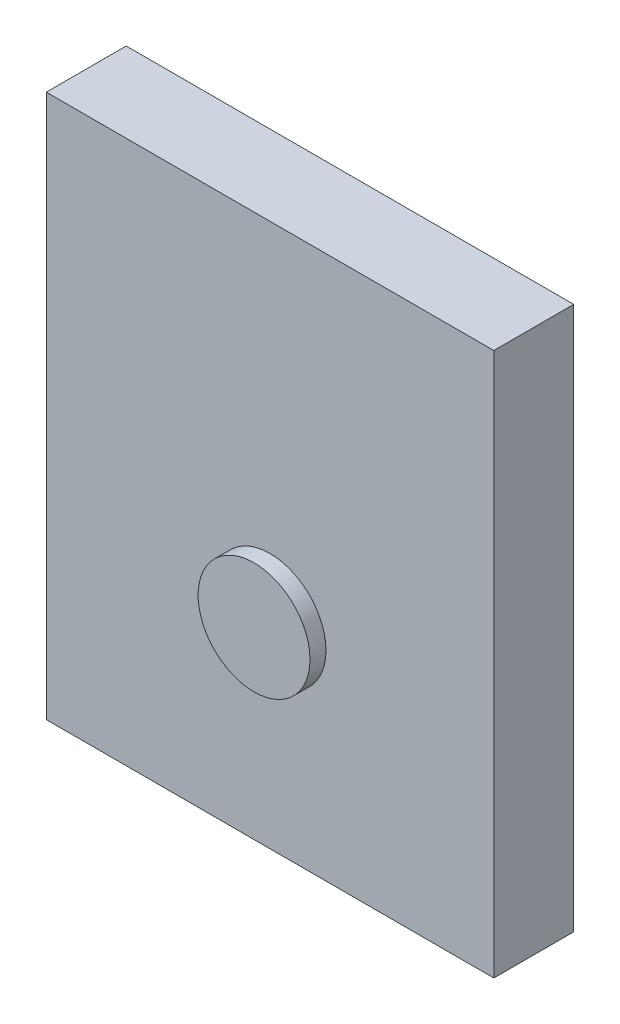
SolidWorks part; units mm, degrees
ref_plane "前视基准面" through (0, 0, 0) normal (0, 0, 1) x (1, 0, 0)
ref_plane "上视基准面" through (0, 0, 0) normal (0, 1, 0) x (1, 0, 0)
ref_plane "右视基准面" through (0, 0, 0) normal (1, 0, 0) x (0, 0, -1)
other "Configuration Table"
sketch "草图1" plane through (0, 0, 0) normal (0, 0, 1) x (1, 0, 0)
  line L1 (8.502, 26.3979) -> (64.502, 26.3979)
  line L2 (8.502, 26.3979) -> (8.502, -41.6021)
  line L3 (8.502, -41.6021) -> (64.502, -41.6021)
  line L4 (64.502, 26.3979) -> (64.502, -41.6021)
  dimension "D1" = 56
  dimension "D2" = 68
extrude "凸台-拉伸1" add sketch "草图1" along normal blind 10
sketch "草图2" plane through (0, 0, 10) normal (0, 0, 1) x (1, 0, 0)
  line L0 (8.502, -41.6021) -> (64.502, -41.6021) construction
  circle A0 centre (36.502, -16.6021) radius 7
  point P2 (0, 0)
  point P5 (36.502, -41.6021)
  dimension "D1" = 14
  dimension "D2" = 25
extrude "凸台-拉伸2" add sketch "草图2" along normal blind 2
